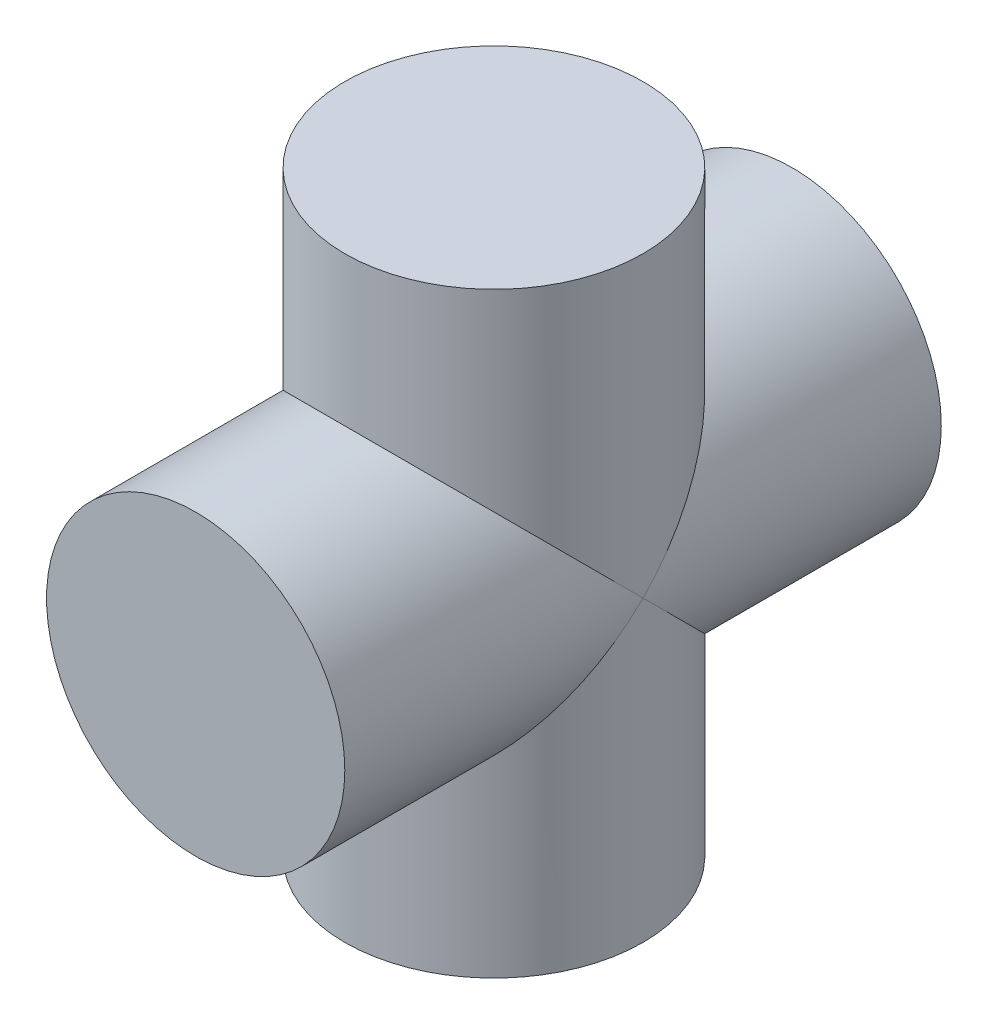
SolidWorks part; units mm, degrees
ref_plane "Front Plane" through (0, 0, 0) normal (0, 0, 1) x (1, 0, 0)
ref_plane "Top Plane" through (0, 0, 0) normal (0, 1, 0) x (1, 0, 0)
ref_plane "Right Plane" through (0, 0, 0) normal (1, 0, 0) x (0, 0, -1)
sketch "Sketch1" plane through (0, 0, 0) normal (0, 0, 1) x (1, 0, 0)
  circle A0 centre (0, 0) radius 5
  dimension "D1" = 10
extrude "Boss-Extrude1" add sketch "Sketch1" along normal mid plane 20
sketch "Sketch2" plane through (0, 0, 0) normal (0, 1, 0) x (1, 0, 0)
  circle A0 centre (0, 0) radius 5
  dimension "D1" = 10
extrude "Boss-Extrude2" add sketch "Sketch2" along normal mid plane 20
